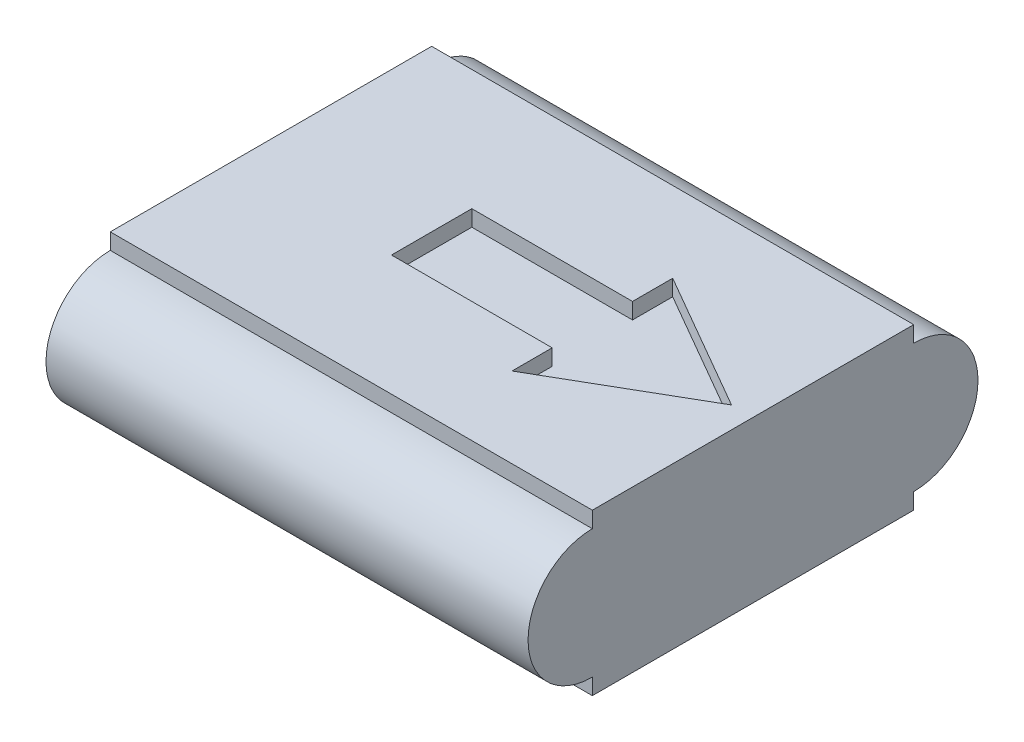
SolidWorks part; units mm, degrees
ref_plane "Front Plane" through (0, 0, 0) normal (0, 0, 1) x (1, 0, 0)
ref_plane "Top Plane" through (0, 0, 0) normal (0, 1, 0) x (1, 0, 0)
ref_plane "Right Plane" through (0, 0, 0) normal (1, 0, 0) x (0, 0, -1)
sketch "Sketch1" plane through (0, 0, 0) normal (0, 1, 0) x (1, 0, 0)
  line L1 (150, -100) -> (-150, -100)
  line L2 (150, -100) -> (150, 100)
  line L3 (150, 100) -> (-150, 100)
  line L4 (-150, -100) -> (-150, 100)
  line L5 (150, -100) -> (-150, 100) construction
  line L6 (150, 100) -> (-150, -100) construction
  point P0 (0, 0)
  dimension "D1" = 300
  dimension "D2" = 200
extrude "Boss-Extrude2" add sketch "Sketch1" along normal blind 100
sketch "Sketch2" plane through (-150, 0, 0) normal (-1, 0, 0) x (0, 0, 1)
  line L0 (100, 100) -> (100, 0) construction
  line L1 (-100, 100) -> (-100, 0) construction
  circle A0 centre (100, 50) radius 40
  circle A1 centre (-100, 50) radius 40
  dimension "D1" = 80
extrude "Boss-Extrude3" add sketch "Sketch2" against normal up to surface (300 mm away) up to face at (150, 50, 0)
sketch "Sketch3" plane through (0, 100, 0) normal (0, 1, 0) x (1, 0, 0)
  line L0 (50, 25) -> (50, 50)
  line L1 (50, -25) -> (-50, -25) construction
  line L2 (50, -25) -> (50, 25) construction
  line L3 (50, 25) -> (-50, 25) construction
  line L4 (-50, -25) -> (-50, 25) construction
  line L5 (50, -25) -> (-50, 25) construction
  line L6 (50, 25) -> (-50, -25) construction
  line L7 (50, 50) -> (136.6025, 0)
  line L8 (136.6025, 0) -> (50, -50)
  line L9 (50, -50) -> (50, -25)
  line L10 (50, -25) -> (-50, -25)
  line L11 (-50, -25) -> (-50, 25)
  line L12 (-50, 25) -> (50, 25)
  point P0 (0, 0)
  point P5 (44.3151, -25)
  point P11 (0, 0)
  point P12 (0, 0)
  point P13 (75, 49.7546)
  dimension "D1" = 50
  dimension "D2" = 100
  dimension "D3" = 100
  dimension "D4" = 60
extrude "Cut-Extrude1" cut sketch "Sketch3" against normal blind 10
